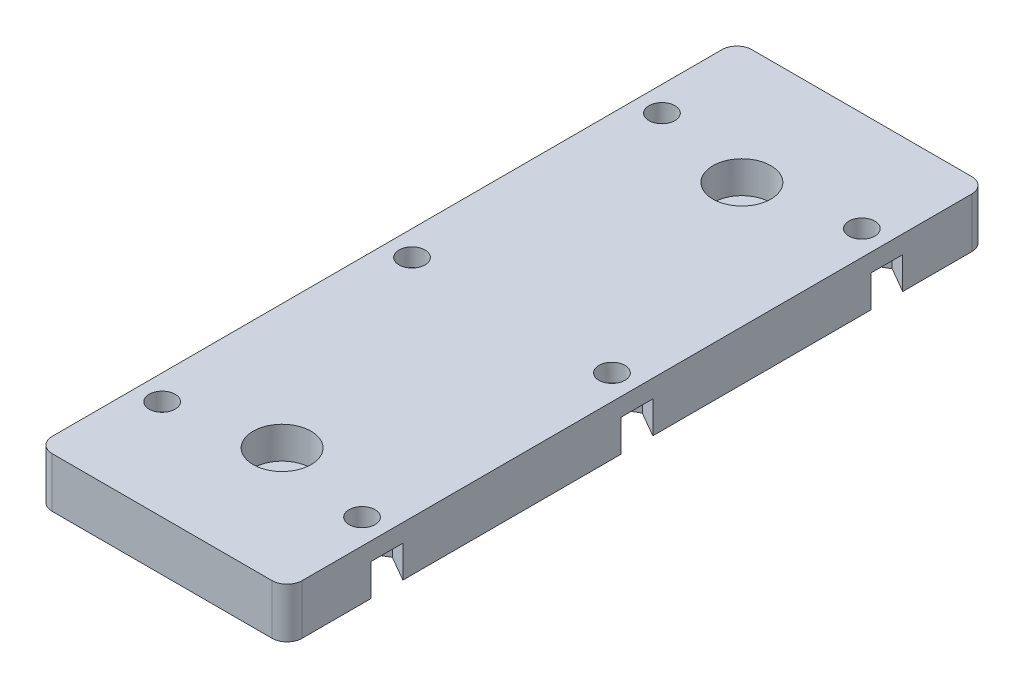
SolidWorks part; units mm, degrees
ref_plane "前视基准面" through (0, 0, 0) normal (0, 0, 1) x (1, 0, 0)
ref_plane "上视基准面" through (0, 0, 0) normal (0, 1, 0) x (1, 0, 0)
ref_plane "右视基准面" through (0, 0, 0) normal (1, 0, 0) x (0, 0, -1)
sketch "草图1" plane through (0, 0, 0) normal (0, 1, 0) x (1, 0, 0)
  line L0 (0, -23) -> (0, 23) construction
  line L1 (-12.5, -35) -> (12.5, -35)
  line L2 (-12.5, -35) -> (-12.5, 35)
  line L3 (-12.5, 35) -> (12.5, 35)
  line L4 (12.5, -35) -> (12.5, 35)
  line L5 (-12.5, -35) -> (12.5, 35) construction
  line L6 (-12.5, 35) -> (12.5, -35) construction
  circle A0 centre (10, 25) radius 1.3
  circle A4 centre (10, 0) radius 1.3
  circle A5 centre (10, -25) radius 1.3
  circle A10 centre (0, 23) radius 1.65
  circle A11 centre (0, -23) radius 1.65
  circle A12 centre (-10, 25) radius 1.3
  circle A13 centre (-10, 0) radius 1.3
  circle A14 centre (-10, -25) radius 1.3
  point P0 (0, 0)
  point P15 (0, 0)
  dimension "D5" = 2.6
  dimension "D7" = 3.3
  dimension "D1" = 25
  dimension "D2" = 70
  dimension "D3" = 10
  dimension "D4" = 10
  dimension "D8" = 12
  dimension "D6" = 3
extrude "凸台-拉伸1" add sketch "草图1" along normal blind 5
sketch "草图2" plane through (0, 5, 0) normal (0, 1, 0) x (1, 0, 0)
  circle A0 centre (0, 23) radius 2.9
  circle A1 centre (0, -23) radius 2.9
  dimension "D1" = 5.8
extrude "切除-拉伸1" cut sketch "草图2" against normal offset from surface (3.2 mm away) 1.8 up to face at (-10, 0, -1.3)
sketch "草图3" plane through (0, 0, 0) normal (0, -1, 0) x (1, 0, 0)
  line L1 (-7.375, 23.4845) -> (-7.375, 26.5155)
  line L2 (-7.375, 26.5155) -> (-10, 28.0311)
  line L3 (-10, 28.0311) -> (-12.625, 26.5155)
  line L4 (-12.625, 26.5155) -> (-12.625, 23.4845)
  line L5 (-12.625, 23.4845) -> (-10, 21.9689)
  line L6 (-10, 21.9689) -> (-7.375, 23.4845)
  line L7 (10, 28.0311) -> (7.375, 26.5155)
  line L8 (7.375, 26.5155) -> (7.375, 23.4845)
  line L9 (7.375, 23.4845) -> (10, 21.9689)
  line L10 (10, 21.9689) -> (12.625, 23.4845)
  line L11 (12.625, 23.4845) -> (12.625, 26.5155)
  line L12 (12.625, 26.5155) -> (10, 28.0311)
  line L13 (10, 3.0311) -> (7.375, 1.5155)
  line L14 (7.375, 1.5155) -> (7.375, -1.5155)
  line L15 (7.375, -1.5155) -> (10, -3.0311)
  line L16 (10, -3.0311) -> (12.625, -1.5155)
  line L17 (12.625, -1.5155) -> (12.625, 1.5155)
  line L18 (12.625, 1.5155) -> (10, 3.0311)
  line L19 (-10, 3.0311) -> (-12.625, 1.5155)
  line L20 (-12.625, 1.5155) -> (-12.625, -1.5155)
  line L21 (-12.625, -1.5155) -> (-10, -3.0311)
  line L22 (-10, -3.0311) -> (-7.375, -1.5155)
  line L23 (-7.375, -1.5155) -> (-7.375, 1.5155)
  line L24 (-7.375, 1.5155) -> (-10, 3.0311)
  line L25 (-7.375, -26.5155) -> (-7.375, -23.4845)
  line L26 (-7.375, -23.4845) -> (-10, -21.9689)
  line L27 (-10, -21.9689) -> (-12.625, -23.4845)
  line L28 (-12.625, -23.4845) -> (-12.625, -26.5155)
  line L29 (-12.625, -26.5155) -> (-10, -28.0311)
  line L30 (-10, -28.0311) -> (-7.375, -26.5155)
  line L31 (10, -21.9689) -> (7.375, -23.4845)
  line L32 (7.375, -23.4845) -> (7.375, -26.5155)
  line L33 (7.375, -26.5155) -> (10, -28.0311)
  line L34 (10, -28.0311) -> (12.625, -26.5155)
  line L35 (12.625, -26.5155) -> (12.625, -23.4845)
  line L36 (12.625, -23.4845) -> (10, -21.9689)
  circle A6 centre (-10, 25) radius 2.625 construction
  circle A7 centre (10, 25) radius 2.625 construction
  circle A8 centre (10, 0) radius 2.625 construction
  circle A9 centre (-10, 0) radius 2.625 construction
  circle A10 centre (-10, -25) radius 2.625 construction
  circle A11 centre (10, -25) radius 2.625 construction
  dimension "D1" = 5.25
extrude "切除-拉伸2" cut sketch "草图3" against normal offset from surface (3.2 mm away) 1.8 up to face at (0, 5, -20.1)
fillet "圆角1" radius 1.5 4 edges at (12.5, 2.5, 35) (-12.5, 2.5, 35) (-12.5, 2.5, -35) (12.5, 2.5, -35)
sketch "草图4" plane through (0, 0, 0) normal (1, 0, 0) x (0, 0, -1)
  line L0 (-34, 0) -> (-27, 0)
  line L1 (-33.5, 0) -> (-26.5877, 0) construction
  line L2 (-27, 0) -> (-29, -2)
  line L3 (-29, -2) -> (-32, -2)
  line L4 (-32, -2) -> (-34, 0)
  line L5 (0, 0) -> (0, 10.4173) construction
  line L6 (29, -2) -> (32, -2)
  line L7 (27, 0) -> (29, -2)
  line L8 (34, 0) -> (27, 0)
  line L9 (32, -2) -> (34, 0)
  point P13 (-26.9327, 0)
  dimension "D1" = 2
  dimension "D2" = 135
  dimension "D3" = 7
  dimension "D4" = 27
extrude "凸台-拉伸2" add sketch "草图4" along normal mid plane 6
